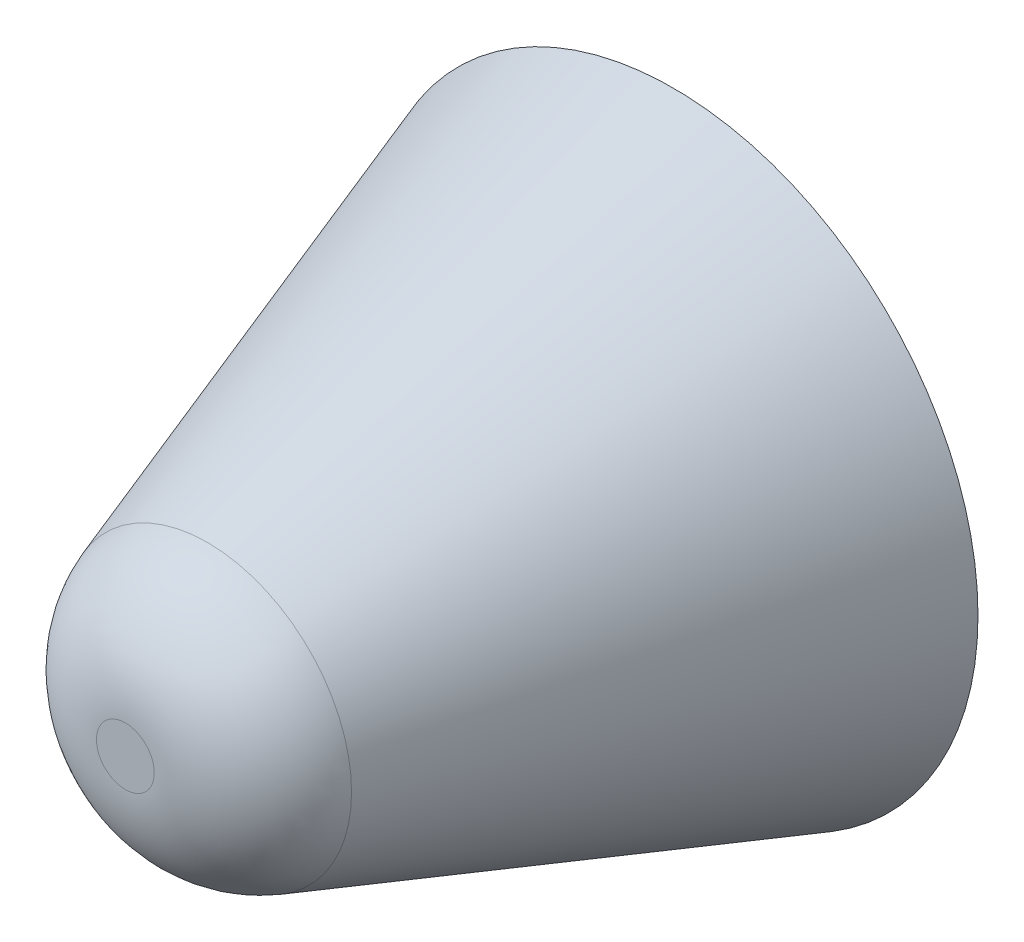
SolidWorks part; units mm, degrees
ref_plane "Ön Düzlem" through (0, 0, 0) normal (0, 0, 1) x (1, 0, 0)
ref_plane "Üst Düzlem" through (0, 0, 0) normal (0, 1, 0) x (1, 0, 0)
ref_plane "Sağ Düzlem" through (0, 0, 0) normal (1, 0, 0) x (0, 0, -1)
sketch "Sketch1" plane through (0, 0, 0) normal (0, 0, 1) x (1, 0, 0)
  circle A0 centre (0, 0) radius 0.5
  dimension "D1" = 1
extrude "Boss-Extrude1" add sketch "Sketch1" along normal blind 0.9 draft 19
fillet "Fillet1" radius 0.2 1 edges at (0.1901, 0, 0.9)
